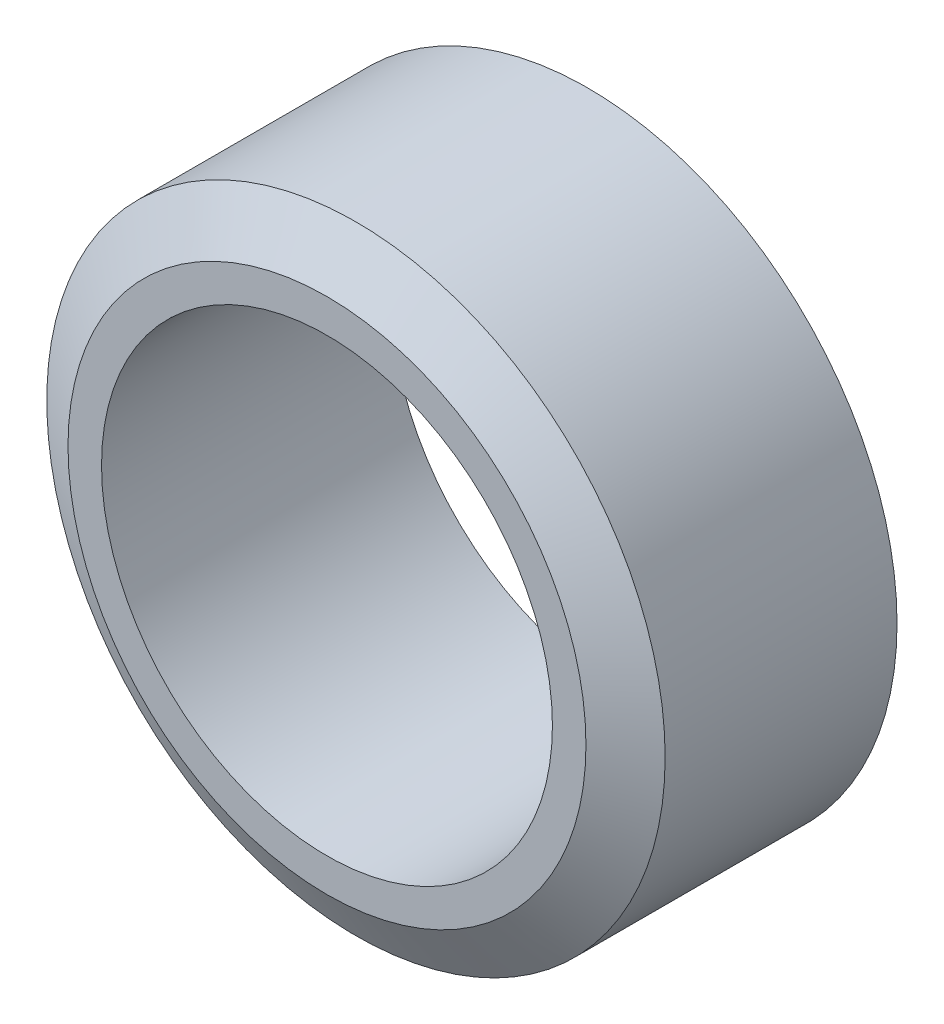
SolidWorks part; units mm, degrees
ref_plane "Plan de face" through (0, 0, 0) normal (0, 0, 1) x (1, 0, 0)
ref_plane "Plan de dessus" through (0, 0, 0) normal (0, 1, 0) x (1, 0, 0)
ref_plane "Plan de droite" through (0, 0, 0) normal (1, 0, 0) x (0, 0, -1)
sketch "Esquisse1" plane through (0, 0, 0) normal (0, 0, 1) x (1, 0, 0)
  circle A0 centre (0, 0) radius 9.6
  circle A1 centre (0, 0) radius 7
  dimension "D1" = 14
  dimension "D2" = 19.2
extrude "Boss.-Extru.1" add sketch "Esquisse1" along normal blind 9
chamfer "Chanfrein5" distance 0.9 angle 60 1 edges at (9.6, 0, 9)
chamfer "Chanfrein9" distance 0.9 angle 60 1 edges at (9.6, 0, 0)
